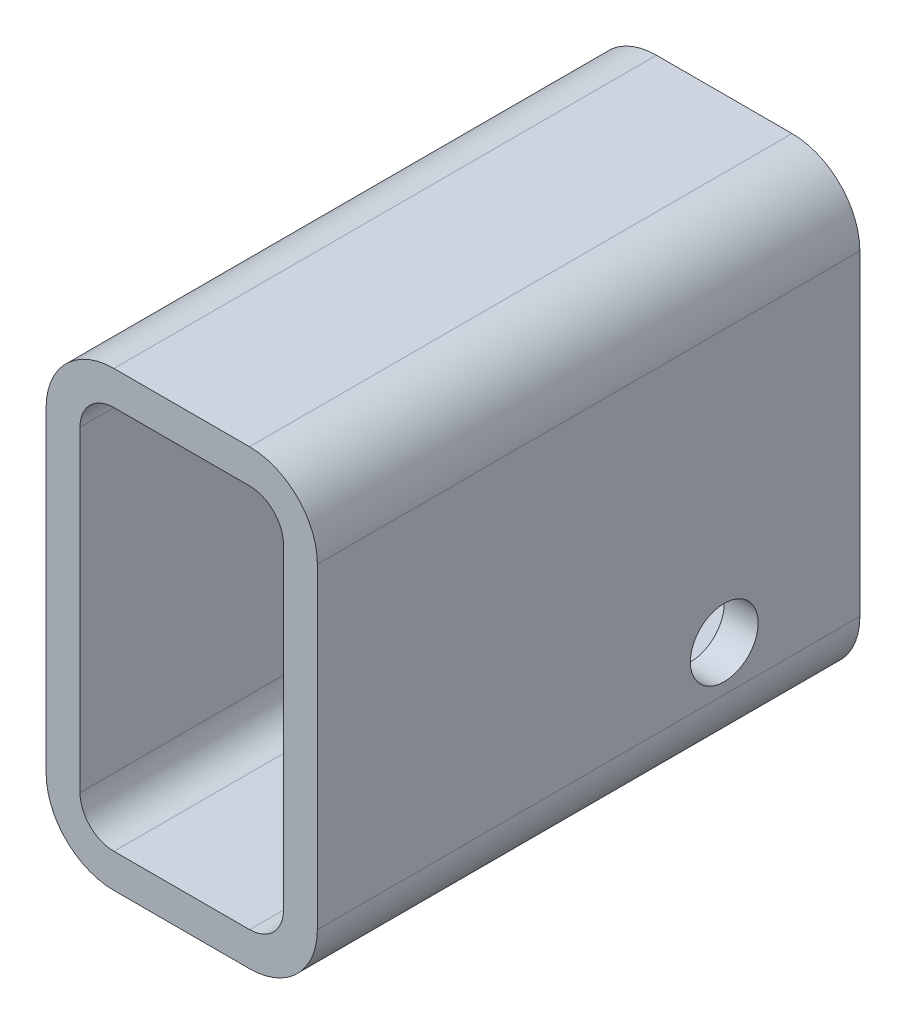
SolidWorks part; units mm, degrees
ref_plane "Plane1" through (0, 0, 0) normal (0, 0, 1) x (1, 0, 0)
ref_plane "Plane2" through (0, 0, 0) normal (0, 1, 0) x (1, 0, 0)
ref_plane "Plane3" through (0, 0, 0) normal (1, 0, 0) x (0, 0, -1)
sketch "Sketch1" plane through (0, 0, 0) normal (0, 0, 1) x (1, 0, 0)
  line L0 (19.05, 9.525) -> (57.15, 9.525)
  line L1 (9.525, 19.05) -> (9.525, 107.95)
  line L2 (57.15, 117.475) -> (19.05, 117.475)
  line L3 (66.675, 107.95) -> (66.675, 19.05)
  line L4 (19.05, 0) -> (57.15, 0)
  line L5 (0, 19.05) -> (0, 107.95)
  line L6 (57.15, 127) -> (19.05, 127)
  line L7 (76.2, 107.95) -> (76.2, 19.05)
  arc A0 (76.2, 107.95) -> (57.15, 127) centre (57.15, 107.95) ccw
  arc A1 (57.15, 0) -> (76.2, 19.05) centre (57.15, 19.05) ccw
  arc A2 (0, 19.05) -> (19.05, 0) centre (19.05, 19.05) ccw
  arc A3 (19.05, 127) -> (0, 107.95) centre (19.05, 107.95) ccw
  arc A4 (19.05, 117.475) -> (9.525, 107.95) centre (19.05, 107.95) ccw
  arc A5 (66.675, 107.95) -> (57.15, 117.475) centre (57.15, 107.95) ccw
  arc A6 (57.15, 9.525) -> (66.675, 19.05) centre (57.15, 19.05) ccw
  arc A7 (9.525, 19.05) -> (19.05, 9.525) centre (19.05, 19.05) ccw
  dimension "D1" = 19.05
  dimension "Thickness" = 9.525
  dimension "V_leg" = 127
  dimension "H_leg" = 76.2
extrude "BaseTubeR" add sketch "Sketch1" along normal mid plane 152.4
sketch "Sketch2" plane through (0, 0, 0) normal (-1, 0, 0) x (0, 0, 1)
  line L0 (-76.2, 107.95) -> (-76.2, 19.05) construction
  line L1 (76.2, 19.05) -> (-76.2, 19.05) construction
  circle A0 centre (-38.1, 31.75) radius 5.5562
  dimension "D1" = 11.1125
  dimension "D3" = 12.7
  dimension "D2" = 38.1
sketch "Sketch3" plane through (76.2, 0, 0) normal (1, 0, 0) x (0, 0, -1)
  line L0 (76.2, 19.05) -> (76.2, 107.95) construction
  line L1 (-76.2, 19.05) -> (76.2, 19.05) construction
  circle A0 centre (38.1, 31.75) radius 9.525
  dimension "D1" = 19.05
  dimension "D2" = 38.1
  dimension "D3" = 12.7
extrude "Cut-Extrude2" cut sketch "Sketch3" against normal up to next
equation "\"D1@Sketch1\" = \"Thickness@Sketch1\" * 2"
